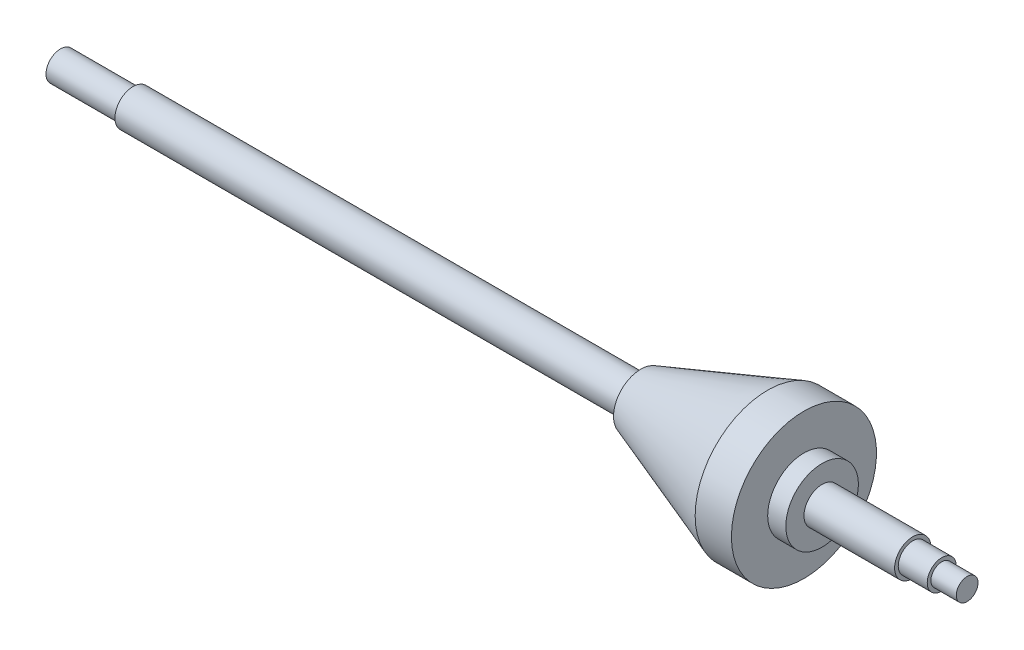
SolidWorks part; units mm, degrees
ref_plane "Front Plane" through (0, 0, 0) normal (0, 0, 1) x (1, 0, 0)
ref_plane "Top Plane" through (0, 0, 0) normal (0, 1, 0) x (1, 0, 0)
ref_plane "Right Plane" through (0, 0, 0) normal (1, 0, 0) x (0, 0, -1)
sketch "Sketch2" plane through (0, 0, 0) normal (0, 0, 1) x (1, 0, 0)
  line L0 (0, 0) -> (891.2204, 0) construction
  line L1 (0, 0) -> (0, 4)
  line L2 (0, 4) -> (20, 4)
  line L3 (20, 4) -> (20, 5)
  line L4 (20, 5) -> (130, 5)
  line L5 (130, 5) -> (160, 5)
  line L6 (160, 5) -> (160, 7.5)
  line L7 (160, 7.5) -> (195, 20)
  line L8 (195, 20) -> (205, 20)
  line L9 (205, 20) -> (205, 10)
  line L10 (205, 10) -> (210, 10)
  line L11 (210, 10) -> (210, 5)
  line L12 (210, 5) -> (235, 5)
  line L13 (235, 5) -> (235, 4)
  line L14 (235, 4) -> (243, 4)
  line L15 (243, 4) -> (243, 3)
  line L16 (243, 3) -> (250, 3)
  line L17 (891.2204, 0) -> (1132.0748, 0) construction
  line L18 (250, 3) -> (250, 0)
  line L19 (0, 0) -> (250, 0)
  dimension "D1" = 6
  dimension "D2" = 8
  dimension "D3" = 10
  dimension "D4" = 20
  dimension "D5" = 5
  dimension "D6" = 30
  dimension "D7" = 38
  dimension "D8" = 45
  dimension "D9" = 8
  dimension "D10" = 10
  dimension "D11" = 15
  dimension "D12" = 40
  dimension "D13" = 10
  dimension "D14" = 45
  dimension "D15" = 75
  dimension "D16" = 185
  dimension "D17" = 20
revolve "Revolve6" add sketch "Sketch2" angle 360 about L19
